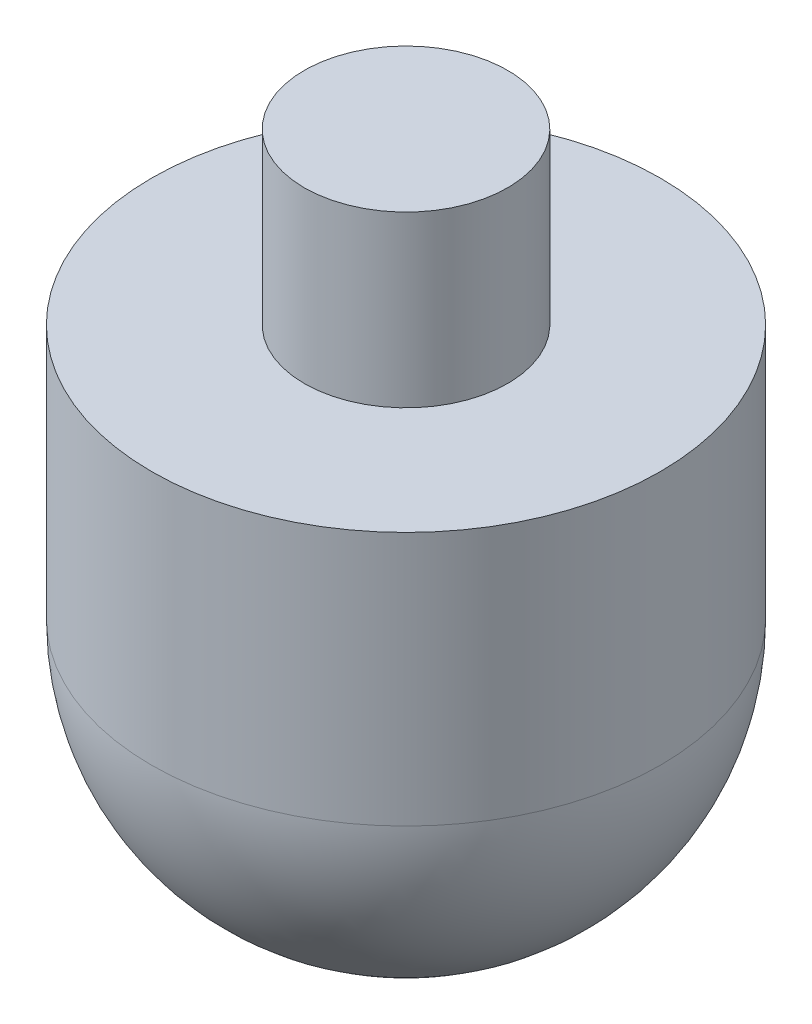
SolidWorks part; units mm, degrees
ref_plane "Front Plane" through (0, 0, 0) normal (0, 0, 1) x (1, 0, 0)
ref_plane "Top Plane" through (0, 0, 0) normal (0, 1, 0) x (1, 0, 0)
ref_plane "Right Plane" through (0, 0, 0) normal (1, 0, 0) x (0, 0, -1)
sketch "Sketch1" plane through (0, 0, 0) normal (0, 0, 1) x (1, 0, 0)
  line L1 (0, 88.3227) -> (0, -46.5356) construction
  line L2 (15, -25) -> (15, -10)
  line L3 (15, -10) -> (6, -10)
  line L4 (6, -10) -> (6, 0)
  line L5 (6, 0) -> (0, 0)
  line L6 (0, 0) -> (0, -40)
  arc A0 (0, -40) -> (15, -25) centre (0, -25) ccw
  dimension "D1" = 12
  dimension "D2" = 15
  dimension "D3" = 10
  dimension "D4" = 30
revolve "Revolve2" add sketch "Sketch1" angle 360 about L1
